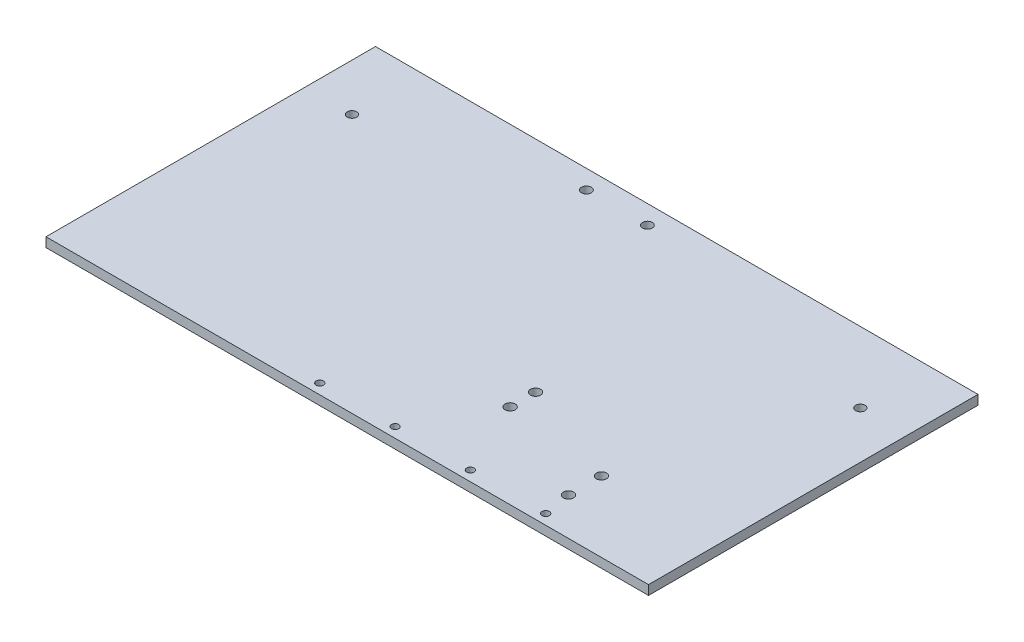
SolidWorks part; units mm, degrees
material "PC High Viscosity"
ref_plane "Front Plane" through (0, 0, 0) normal (0, 0, 1) x (1, 0, 0)
ref_plane "Top Plane" through (0, 0, 0) normal (0, 1, 0) x (1, 0, 0)
ref_plane "Right Plane" through (0, 0, 0) normal (1, 0, 0) x (0, 0, -1)
sketch "Sketch1" plane through (0, 0, 0) normal (0, 1, 0) x (1, 0, 0)
  line L1 (203.2, -111.125) -> (-203.2, -111.125)
  line L2 (203.2, -111.125) -> (203.2, 111.125)
  line L3 (203.2, 111.125) -> (-203.2, 111.125)
  line L4 (-203.2, -111.125) -> (-203.2, 111.125)
  line L5 (203.2, -111.125) -> (-203.2, 111.125) construction
  line L6 (203.2, 111.125) -> (-203.2, -111.125) construction
  point P0 (0, 0)
  dimension "D1" = 406.4
  dimension "D2" = 222.25
extrude "Boss-Extrude1" add sketch "Sketch1" along normal blind 6.35
sketch "Sketch2" plane through (0, 6.35, 0) normal (0, 1, 0) x (1, 0, 0)
  line L0 (-203.2, 111.125) -> (-203.2, -111.125) construction
  line L1 (203.2, 111.125) -> (-203.2, 111.125) construction
  line L2 (203.2, 111.125) -> (-203.2, 111.125) construction
  line L3 (-203.2, 111.125) -> (-203.2, -111.125) construction
  line L4 (203.2, -111.125) -> (203.2, 111.125) construction
  circle A0 centre (-48.26, 98.425) radius 3.302
  circle A2 centre (-7.112, 98.425) radius 3.302
  circle A3 centre (-171.45, 63.5) radius 3.175
  circle A4 centre (171.45, 63.5) radius 3.175
  dimension "D2" = 6.604
  dimension "D4" = 6.35
  dimension "D1" = 154.94
  dimension "D3" = 12.7
  dimension "D5" = 47.625
  dimension "D6" = 31.75
  dimension "D7" = 31.75
  dimension "D8" = 41.148
extrude "Cut-Extrude1" cut sketch "Sketch2" against normal blind 6.35
sketch "Sketch3" plane through (0, 0, 0) normal (0, -1, 0) x (1, 0, 0)
  line L1 (203.2, 111.125) -> (203.2, -111.125) construction
  line L2 (-203.2, 111.125) -> (203.2, 111.125) construction
  circle A0 centre (127, 104.267) radius 2.4638
  circle A1 centre (76.2, 104.267) radius 2.4638
  circle A2 centre (25.4, 104.267) radius 2.4638
  circle A3 centre (-25.4, 104.267) radius 2.4638
  dimension "D6" = 4.9276
  dimension "D1" = 76.2
  dimension "D2" = 6.858
  dimension "D3" = 50.8
  dimension "D4" = 50.8
  dimension "D5" = 50.8
extrude "Cut-Extrude2" cut sketch "Sketch3" against normal through all
sketch "Sketch4" plane through (0, 0, 0) normal (0, -1, 0) x (1, 0, 0)
  line L0 (-203.2, 111.125) -> (203.2, 111.125) construction
  line L1 (203.2, 111.125) -> (203.2, -111.125) construction
  circle A0 centre (52.705, 36.83) radius 3.429
  circle A1 centre (52.705, 53.975) radius 3.429
  circle A2 centre (123.825, 63.5) radius 3.429
  circle A3 centre (123.825, 85.725) radius 3.429
  dimension "D1" = 6.858
  dimension "D2" = 25.4
  dimension "D3" = 79.375
  dimension "D4" = 22.225
  dimension "D5" = 57.15
  dimension "D6" = 17.145
  dimension "D7" = 71.12
extrude "Cut-Extrude3" cut sketch "Sketch4" against normal up to next
